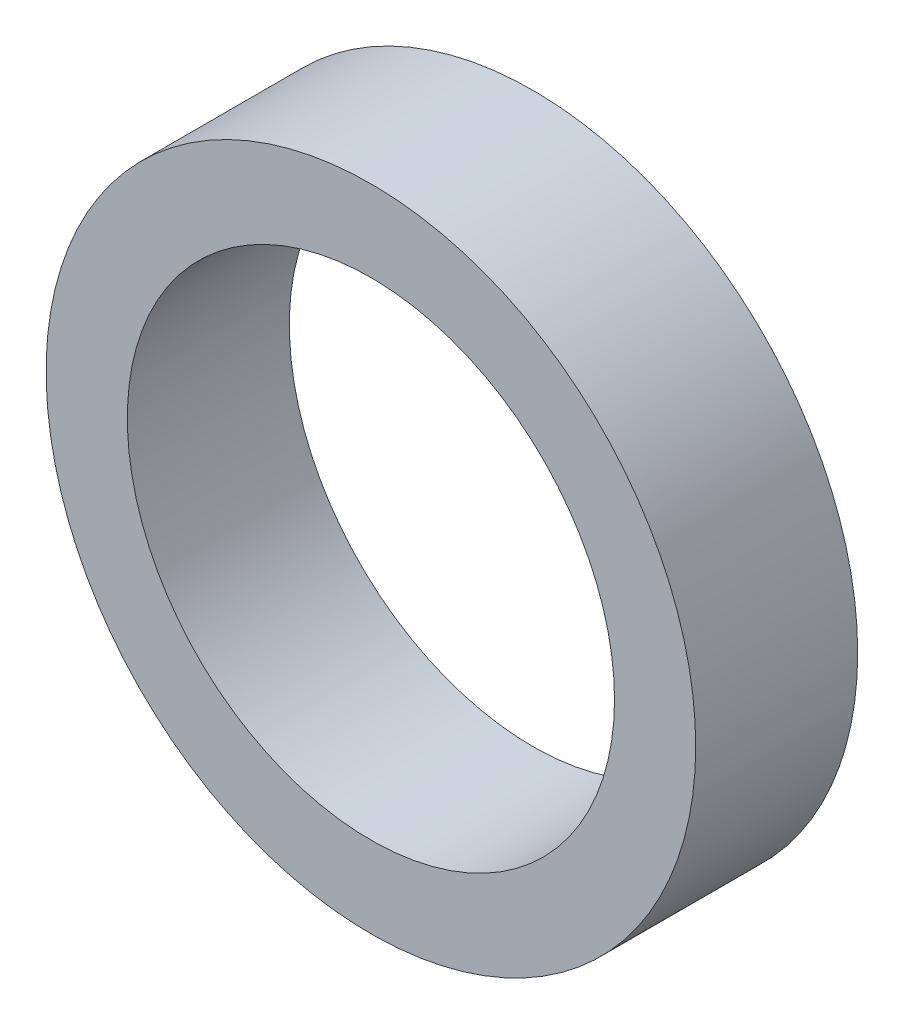
SolidWorks part; units mm, degrees
material "6061 Alloy"
ref_plane "Front Plane" through (0, 0, 0) normal (0, 0, 1) x (1, 0, 0)
ref_plane "Top Plane" through (0, 0, 0) normal (0, 1, 0) x (1, 0, 0)
ref_plane "Right Plane" through (0, 0, 0) normal (1, 0, 0) x (0, 0, -1)
sketch "Sketch1" plane through (0, 0, 0) normal (0, 0, 1) x (1, 0, 0)
  circle A0 centre (0, 0) radius 4.7625
  circle A1 centre (0, 0) radius 6.35
  dimension "D1" = 9.525
  dimension "D2" = 12.7
extrude "Boss-Extrude1" add sketch "Sketch1" along normal blind 3.1665
